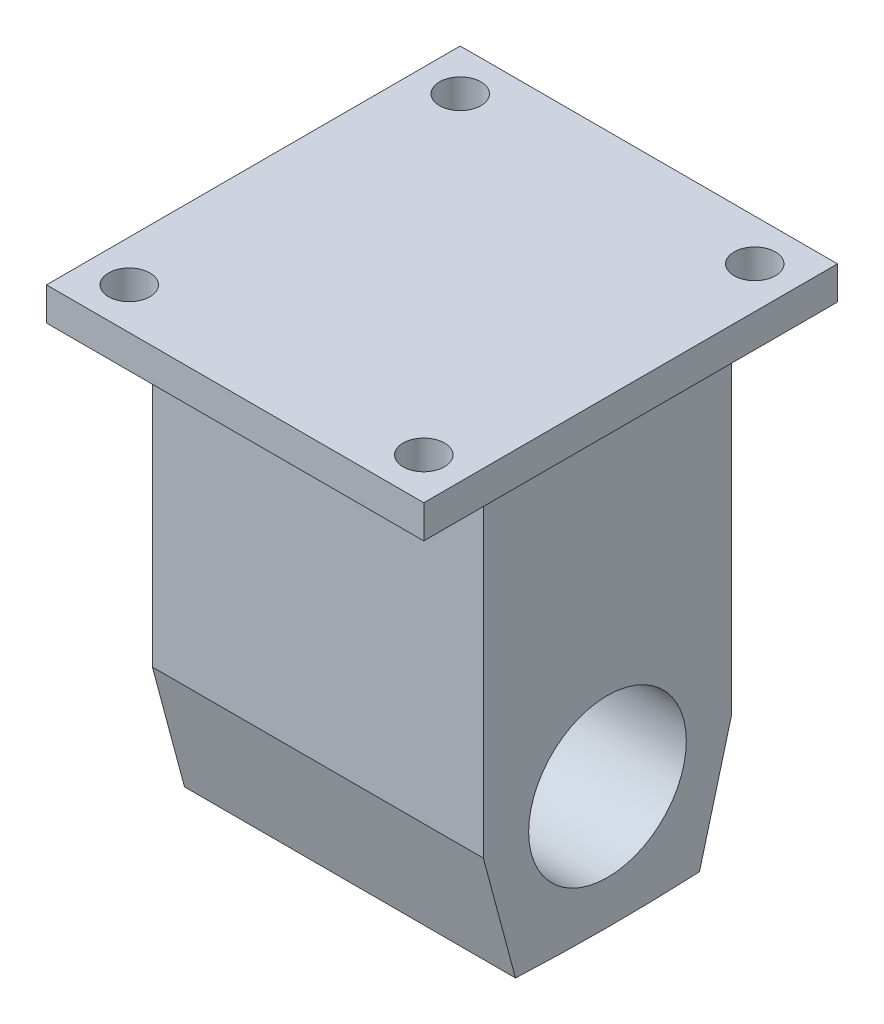
SolidWorks part; units mm, degrees
material "ABS"
ref_plane "Front Plane" through (0, 0, 0) normal (0, 0, 1) x (1, 0, 0)
ref_plane "Top Plane" through (0, 0, 0) normal (0, 1, 0) x (1, 0, 0)
ref_plane "Right Plane" through (0, 0, 0) normal (1, 0, 0) x (0, 0, -1)
sketch "Sketch1" plane through (0, 0, 0) normal (0, 1, 0) x (1, 0, 0)
  line L1 (-25.4, -19.05) -> (25.4, -19.05)
  line L2 (-25.4, -19.05) -> (-25.4, 19.05)
  line L3 (-25.4, 19.05) -> (25.4, 19.05)
  line L4 (25.4, -19.05) -> (25.4, 19.05)
  line L5 (-25.4, -19.05) -> (25.4, 19.05) construction
  line L6 (-25.4, 19.05) -> (25.4, -19.05) construction
  point P0 (0, 0)
extrude "Boss-Extrude1" add sketch "Sketch1" along normal blind 50.292
sketch "Sketch2" plane through (25.4, 0, 0) normal (1, 0, 0) x (0, 0, -1)
  line L0 (-19.05, 0) -> (-14.1195, -18.4009)
  line L1 (19.05, 0) -> (14.1195, -18.4009)
  line L2 (-19.05, 0) -> (19.05, 0)
  line L3 (-19.05, 0) -> (19.05, 0) construction
  arc A1 (14.1195, -18.4009) -> (-14.1195, -18.4009) centre (0, 281.2546) cw
  dimension "D1" = 19.05
  dimension "D2" = 19.05
  dimension "D3" = 75
  dimension "D4" = 75
extrude "Boss-Extrude2" add sketch "Sketch2" against normal up to vertex (50.8 mm away) contours L0 A1 L1 L2 up to point (-25.4, 0, -19.05)
sketch "Sketch3" plane through (25.4, 0, 0) normal (1, 0, 0) x (0, 0, -1)
  circle A0 centre (0, 0) radius 12.1
extrude "Cut-Extrude1" cut sketch "Sketch3" against normal blind 127 contours A0
sketch "Sketch4" plane through (0, 50.292, 0) normal (0, 1, 0) x (1, 0, 0)
  line L1 (28.956, -31.75) -> (-28.956, -31.75)
  line L2 (28.956, -31.75) -> (28.956, 31.75)
  line L3 (28.956, 31.75) -> (-28.956, 31.75)
  line L4 (-28.956, -31.75) -> (-28.956, 31.75)
  line L5 (28.956, -31.75) -> (-28.956, 31.75) construction
  line L6 (28.956, 31.75) -> (-28.956, -31.75) construction
  point P0 (0, 0)
extrude "Boss-Extrude3" add sketch "Sketch4" along normal blind 5.08
sketch "Sketch5" plane through (0, 55.372, 0) normal (0, 1, 0) x (1, 0, 0)
  line L0 (0, -31.75) -> (0, 31.75) construction
  line L1 (28.956, 31.75) -> (-28.956, 31.75) construction
  line L2 (-28.956, 0) -> (28.956, 0) construction
  line L3 (28.956, -31.75) -> (28.956, 31.75) construction
  line L4 (-22.606, -31.75) -> (-22.606, 31.75) construction
  line L5 (-28.956, 25.4) -> (28.956, 25.4) construction
  line L6 (-28.956, 31.75) -> (-28.956, -31.75) construction
  circle A0 centre (-22.606, 25.4) radius 3.175
  circle A1 centre (-22.606, -25.4) radius 3.175
  circle A2 centre (22.606, 25.4) radius 3.175
  circle A3 centre (22.606, -25.4) radius 3.175
  point P6 (0, 0)
  point P12 (0, 0)
  point P15 (-22.606, 0)
  point P18 (0, 25.4)
  point P20 (-22.606, 25.4)
  dimension "D1" = 6.35
  dimension "D2" = 6.35
  dimension "D3" = 0
extrude "Cut-Extrude2" cut sketch "Sketch5" against normal blind 5.08
